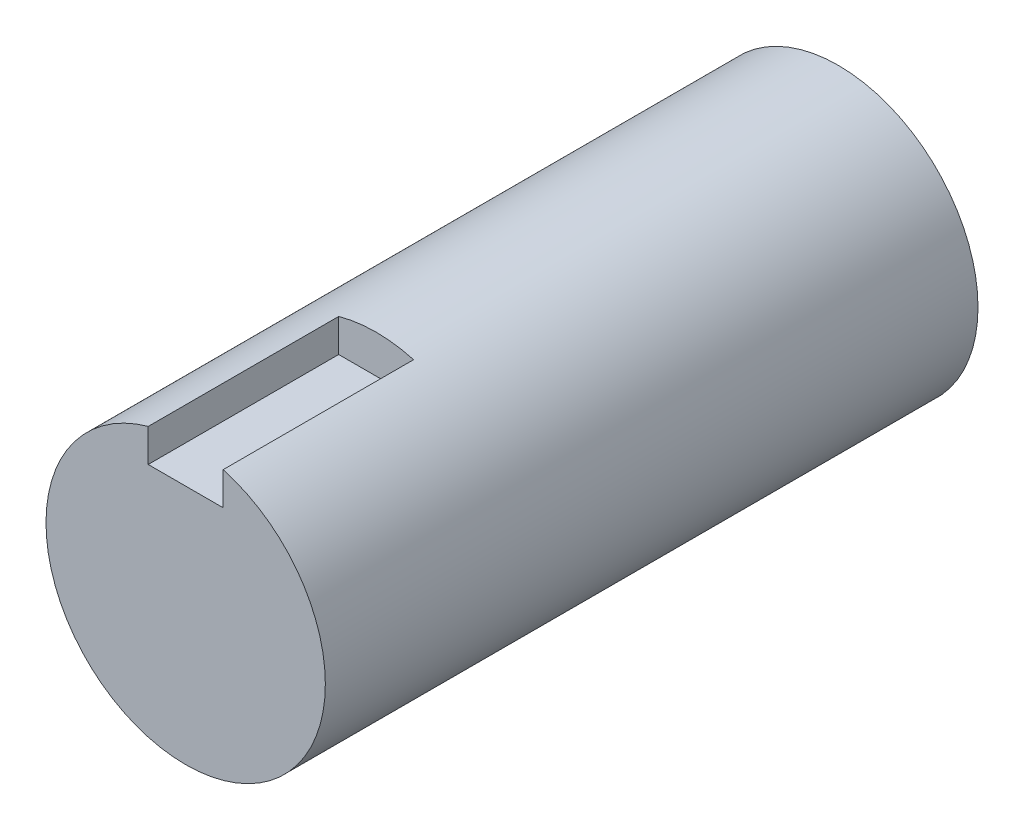
SolidWorks part; units mm, degrees
ref_plane "前视基准面" through (0, 0, 0) normal (0, 0, 1) x (1, 0, 0)
ref_plane "上视基准面" through (0, 0, 0) normal (0, 1, 0) x (1, 0, 0)
ref_plane "右视基准面" through (0, 0, 0) normal (1, 0, 0) x (0, 0, -1)
other "Configuration Table"
sketch "草图1" plane through (0, 0, 0) normal (0, 0, 1) x (1, 0, 0)
  circle A0 centre (0, 0) radius 11
  dimension "D1" = 22
extrude "凸台-拉伸1" add sketch "草图1" along normal blind 51.4
sketch "草图2" plane through (0, 0, 0) normal (1, 0, 0) x (0, 0, -1)
  line L1 (-51.4, 11) -> (-36.4, 11)
  line L2 (-51.4, 11) -> (-51.4, 8)
  line L3 (-51.4, 8) -> (-36.4, 8)
  line L4 (-36.4, 11) -> (-36.4, 8)
  point P4 (-51.4, 11.2365)
  point P5 (-48.8129, 9.6931)
  point P6 (-51.4, 11)
  dimension "D1" = 3
  dimension "D2" = 15
extrude "切除-拉伸1" cut sketch "草图2" against normal mid plane 5.9
